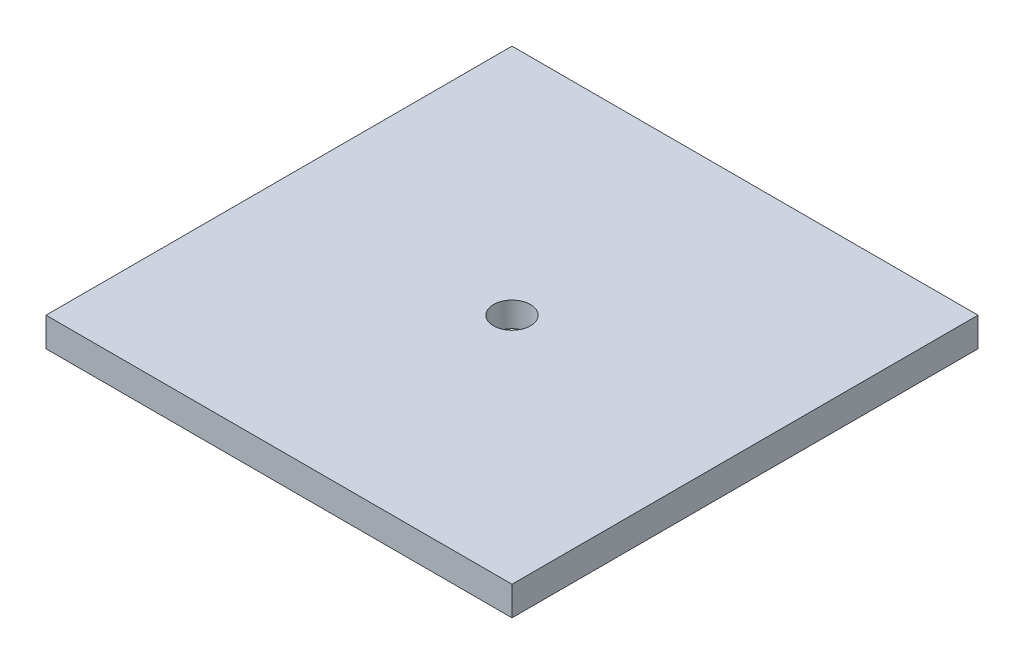
SolidWorks part; units mm, degrees
ref_plane "Front Plane" through (0, 0, 0) normal (0, 0, 1) x (1, 0, 0)
ref_plane "Top Plane" through (0, 0, 0) normal (0, 1, 0) x (1, 0, 0)
ref_plane "Right Plane" through (0, 0, 0) normal (1, 0, 0) x (0, 0, -1)
sketch "Sketch1" plane through (0, 0, 0) normal (0, 1, 0) x (1, 0, 0)
  line L1 (-101.6, 101.6) -> (101.6, 101.6)
  line L2 (-101.6, 101.6) -> (-101.6, -101.6)
  line L3 (-101.6, -101.6) -> (101.6, -101.6)
  line L4 (101.6, 101.6) -> (101.6, -101.6)
  line L5 (-101.6, 101.6) -> (101.6, -101.6) construction
  line L6 (-101.6, -101.6) -> (101.6, 101.6) construction
  point P0 (0, 0)
  dimension "D1" = 203.2
  dimension "D2" = 203.2
extrude "Boss-Extrude1" add sketch "Sketch1" along normal blind 12.7
sketch "Sketch2" plane through (0, 12.7, 0) normal (0, 1, 0) x (1, 0, 0)
  circle A0 centre (0, 0) radius 8.0645
  dimension "D1" = 16.129
extrude "Cut-Extrude1" cut sketch "Sketch2" against normal blind 10.795
